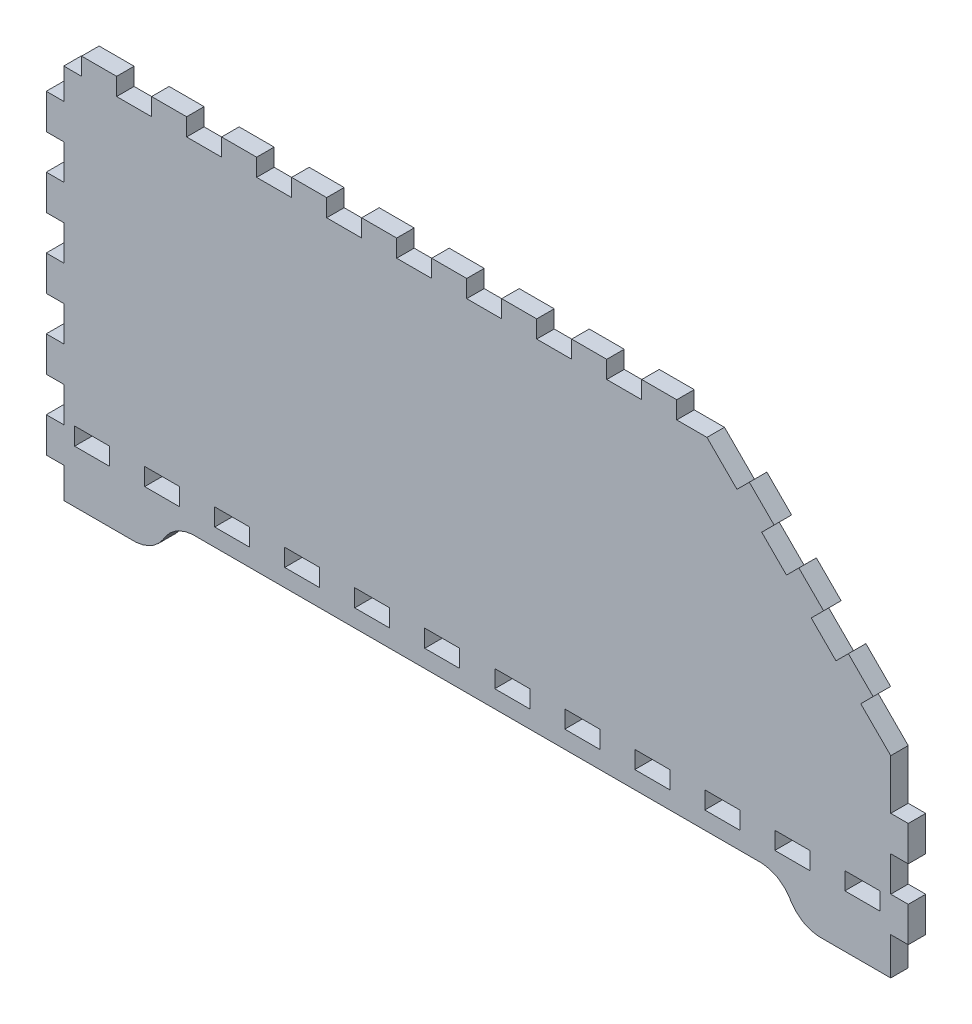
SolidWorks part; units mm, degrees
ref_plane "Front Plane" through (0, 0, 0) normal (0, 0, 1) x (1, 0, 0)
ref_plane "Top Plane" through (0, 0, 0) normal (0, 1, 0) x (1, 0, 0)
ref_plane "Right Plane" through (0, 0, 0) normal (1, 0, 0) x (0, 0, -1)
sketch "Model" plane through (0, 0, 0) normal (0, 0, 1) x (1, 0, 0)
  line L4 (25.3848, 40.3461) -> (19.6701, 40.3461)
  line L5 (19.6701, 40.3461) -> (19.6701, 46.0609)
  line L6 (19.6701, 46.0609) -> (31.0995, 46.0609)
  line L7 (31.0995, 46.0609) -> (31.0995, 40.3461)
  line L8 (31.0995, 40.3461) -> (25.3848, 40.3461)
  line L9 (48.2453, 40.3461) -> (42.5305, 40.3461)
  line L10 (42.5305, 40.3461) -> (42.5305, 46.0609)
  line L11 (42.5305, 46.0609) -> (53.9598, 46.0609)
  line L12 (53.9598, 46.0609) -> (53.9598, 40.3461)
  line L13 (53.9598, 40.3461) -> (48.2453, 40.3461)
  line L14 (71.1055, 40.3461) -> (65.3905, 40.3461)
  line L15 (65.3905, 40.3461) -> (65.3905, 46.0609)
  line L16 (65.3905, 46.0609) -> (76.8203, 46.0609)
  line L17 (76.8203, 46.0609) -> (76.8203, 40.3461)
  line L18 (76.8203, 40.3461) -> (71.1055, 40.3461)
  line L19 (93.9655, 40.3461) -> (88.2495, 40.3461)
  line L20 (88.2495, 40.3461) -> (88.2495, 46.0609)
  line L21 (88.2495, 46.0609) -> (99.6805, 46.0609)
  line L22 (99.6805, 46.0609) -> (99.6805, 40.3461)
  line L23 (99.6805, 40.3461) -> (93.9655, 40.3461)
  line L24 (116.8245, 40.3461) -> (111.1098, 40.3461)
  line L25 (111.1098, 40.3461) -> (111.1098, 46.0609)
  line L26 (111.1098, 46.0609) -> (122.5405, 46.0609)
  line L27 (122.5405, 46.0609) -> (122.5405, 40.3461)
  line L28 (122.5405, 40.3461) -> (116.8245, 40.3461)
  line L29 (139.6848, 40.3461) -> (133.9703, 40.3461)
  line L30 (133.9703, 40.3461) -> (133.9703, 46.0609)
  line L31 (133.9703, 46.0609) -> (145.3995, 46.0609)
  line L32 (145.3995, 46.0609) -> (145.3995, 40.3461)
  line L33 (145.3995, 40.3461) -> (139.6848, 40.3461)
  line L34 (162.5453, 40.3461) -> (156.8305, 40.3461)
  line L35 (156.8305, 40.3461) -> (156.8305, 46.0609)
  line L36 (156.8305, 46.0609) -> (168.2598, 46.0609)
  line L37 (168.2598, 46.0609) -> (168.2598, 40.3461)
  line L38 (168.2598, 40.3461) -> (162.5453, 40.3461)
  line L39 (185.4055, 40.3461) -> (179.6905, 40.3461)
  line L40 (179.6905, 40.3461) -> (179.6905, 46.0609)
  line L41 (179.6905, 46.0609) -> (191.1203, 46.0609)
  line L42 (191.1203, 46.0609) -> (191.1203, 40.3461)
  line L43 (191.1203, 40.3461) -> (185.4055, 40.3461)
  line L44 (208.2655, 40.3461) -> (202.5495, 40.3461)
  line L45 (202.5495, 40.3461) -> (202.5495, 46.0609)
  line L46 (202.5495, 46.0609) -> (213.9805, 46.0609)
  line L47 (213.9805, 46.0609) -> (213.9805, 40.3461)
  line L48 (213.9805, 40.3461) -> (208.2655, 40.3461)
  line L49 (231.1245, 40.3461) -> (225.4098, 40.3461)
  line L50 (225.4098, 40.3461) -> (225.4098, 46.0609)
  line L51 (225.4098, 46.0609) -> (236.8405, 46.0609)
  line L52 (236.8405, 46.0609) -> (236.8405, 40.3461)
  line L53 (236.8405, 40.3461) -> (231.1245, 40.3461)
  line L54 (253.9848, 40.3461) -> (248.2703, 40.3461)
  line L55 (248.2703, 40.3461) -> (248.2703, 46.0609)
  line L56 (248.2703, 46.0609) -> (259.6998, 46.0609)
  line L57 (259.6998, 46.0609) -> (259.6998, 40.3461)
  line L58 (259.6998, 40.3461) -> (253.9848, 40.3461)
  line L59 (276.8448, 40.3461) -> (271.1298, 40.3461)
  line L60 (271.1298, 40.3461) -> (271.1298, 46.0609)
  line L61 (271.1298, 46.0609) -> (282.5598, 46.0609)
  line L62 (282.5598, 46.0609) -> (282.5598, 40.3461)
  line L63 (282.5598, 40.3461) -> (276.8448, 40.3461)
  line L64 (16.1148, 23.2006) -> (38.9748, 23.2006)
  line L65 (38.9748, 23.2006) -> (39.7137, 23.2006)
  line L66 (39.7137, 23.2006) -> (41.9321, 23.5906)
  line L67 (41.9321, 23.5906) -> (44.2542, 24.4809)
  line L68 (44.2542, 24.4809) -> (44.6898, 24.7316)
  line L69 (44.6898, 24.7316) -> (45.1239, 24.9838)
  line L70 (45.1239, 24.9838) -> (47.056, 26.5494)
  line L71 (47.056, 26.5494) -> (48.6227, 28.4813)
  line L72 (48.6227, 28.4813) -> (48.8734, 28.9154)
  line L73 (48.8734, 28.9154) -> (49.1244, 29.3507)
  line L74 (49.1244, 29.3507) -> (50.69, 31.2829)
  line L75 (50.69, 31.2829) -> (52.6217, 32.8483)
  line L76 (52.6217, 32.8483) -> (53.057, 33.099)
  line L77 (53.057, 33.099) -> (53.4914, 33.3499)
  line L78 (53.4914, 33.3499) -> (55.8132, 34.2415)
  line L79 (55.8132, 34.2415) -> (58.0319, 34.6301)
  line L80 (58.0319, 34.6301) -> (58.772, 34.6301)
  line L81 (58.772, 34.6301) -> (243.458, 34.6301)
  line L82 (243.458, 34.6301) -> (244.1966, 34.6301)
  line L83 (244.1966, 34.6301) -> (246.4153, 34.2415)
  line L84 (246.4153, 34.2415) -> (248.7374, 33.3499)
  line L85 (248.7374, 33.3499) -> (249.1725, 33.099)
  line L86 (249.1725, 33.099) -> (249.6068, 32.8483)
  line L87 (249.6068, 32.8483) -> (251.5387, 31.2829)
  line L88 (251.5387, 31.2829) -> (253.1057, 29.3507)
  line L89 (253.1057, 29.3507) -> (253.3566, 28.9154)
  line L90 (253.3566, 28.9154) -> (253.6073, 28.4813)
  line L91 (253.6073, 28.4813) -> (255.1735, 26.5494)
  line L92 (255.1735, 26.5494) -> (257.1039, 24.9838)
  line L93 (257.1039, 24.9838) -> (257.5408, 24.7316)
  line L94 (257.5408, 24.7316) -> (257.9751, 24.4809)
  line L95 (257.9751, 24.4809) -> (260.2967, 23.5906)
  line L96 (260.2967, 23.5906) -> (262.5141, 23.2006)
  line L97 (262.5141, 23.2006) -> (263.2558, 23.2006)
  line L98 (263.2558, 23.2006) -> (286.1158, 23.2006)
  line L99 (286.1158, 23.2006) -> (286.1158, 35.465)
  line L100 (286.1158, 35.465) -> (291.8308, 35.465)
  line L101 (291.8308, 35.465) -> (291.8308, 46.8948)
  line L102 (291.8308, 46.8948) -> (286.1158, 46.8948)
  line L103 (286.1158, 46.8948) -> (286.1158, 58.324)
  line L104 (286.1158, 58.324) -> (291.8308, 58.324)
  line L105 (291.8308, 58.324) -> (291.8308, 69.7547)
  line L106 (291.8308, 69.7547) -> (286.1158, 69.7547)
  line L107 (286.1158, 69.7547) -> (286.1158, 86.0613)
  line L108 (286.1158, 86.0613) -> (276.3215, 95.855)
  line L109 (276.3215, 95.855) -> (280.3627, 99.8967)
  line L110 (280.3627, 99.8967) -> (272.2804, 107.979)
  line L111 (272.2804, 107.979) -> (268.2367, 103.9371)
  line L112 (268.2367, 103.9371) -> (260.1544, 112.0193)
  line L113 (260.1544, 112.0193) -> (264.1981, 116.061)
  line L114 (264.1981, 116.061) -> (256.1158, 124.1417)
  line L115 (256.1158, 124.1417) -> (252.0734, 120.1014)
  line L116 (252.0734, 120.1014) -> (243.9927, 128.1836)
  line L117 (243.9927, 128.1836) -> (248.033, 132.2243)
  line L118 (248.033, 132.2243) -> (239.951, 140.3078)
  line L119 (239.951, 140.3078) -> (235.9091, 136.2662)
  line L120 (235.9091, 136.2662) -> (226.1154, 146.0609)
  line L121 (226.1154, 146.0609) -> (216.2485, 146.0609)
  line L122 (216.2485, 146.0609) -> (216.2485, 151.7757)
  line L123 (216.2485, 151.7757) -> (204.8193, 151.7757)
  line L124 (204.8193, 151.7757) -> (204.8193, 146.0609)
  line L125 (204.8193, 146.0609) -> (193.3885, 146.0609)
  line L126 (193.3885, 146.0609) -> (193.3885, 151.7757)
  line L127 (193.3885, 151.7757) -> (181.959, 151.7757)
  line L128 (181.959, 151.7757) -> (181.959, 146.0609)
  line L129 (181.959, 146.0609) -> (170.5295, 146.0609)
  line L130 (170.5295, 146.0609) -> (170.5295, 151.7757)
  line L131 (170.5295, 151.7757) -> (159.0985, 151.7757)
  line L132 (159.0985, 151.7757) -> (159.0985, 146.0609)
  line L133 (159.0985, 146.0609) -> (147.6692, 146.0609)
  line L134 (147.6692, 146.0609) -> (147.6692, 151.7757)
  line L135 (147.6692, 151.7757) -> (136.2385, 151.7757)
  line L136 (136.2385, 151.7757) -> (136.2385, 146.0609)
  line L137 (136.2385, 146.0609) -> (124.809, 146.0609)
  line L138 (124.809, 146.0609) -> (124.809, 151.7757)
  line L139 (124.809, 151.7757) -> (113.3795, 151.7757)
  line L140 (113.3795, 151.7757) -> (113.3795, 146.0609)
  line L141 (113.3795, 146.0609) -> (101.9485, 146.0609)
  line L142 (101.9485, 146.0609) -> (101.9485, 151.7757)
  line L143 (101.9485, 151.7757) -> (90.5192, 151.7757)
  line L144 (90.5192, 151.7757) -> (90.5192, 146.0609)
  line L145 (90.5192, 146.0609) -> (79.0885, 146.0609)
  line L146 (79.0885, 146.0609) -> (79.0885, 151.7757)
  line L147 (79.0885, 151.7757) -> (67.659, 151.7757)
  line L148 (67.659, 151.7757) -> (67.659, 146.0609)
  line L149 (67.659, 146.0609) -> (56.2295, 146.0609)
  line L150 (56.2295, 146.0609) -> (56.2295, 151.7757)
  line L151 (56.2295, 151.7757) -> (44.7985, 151.7757)
  line L152 (44.7985, 151.7757) -> (44.7985, 146.0609)
  line L153 (44.7985, 146.0609) -> (33.3692, 146.0609)
  line L154 (33.3692, 146.0609) -> (33.3692, 151.7757)
  line L155 (33.3692, 151.7757) -> (21.9384, 151.7757)
  line L156 (21.9384, 151.7757) -> (21.9384, 146.0609)
  line L157 (21.9384, 146.0609) -> (16.1148, 146.0609)
  line L158 (16.1148, 146.0609) -> (16.1148, 136.066)
  line L159 (16.1148, 136.066) -> (10.4001, 136.066)
  line L160 (10.4001, 136.066) -> (10.4001, 124.6353)
  line L161 (10.4001, 124.6353) -> (16.1148, 124.6353)
  line L162 (16.1148, 124.6353) -> (16.1148, 113.2058)
  line L163 (16.1148, 113.2058) -> (10.4001, 113.2058)
  line L164 (10.4001, 113.2058) -> (10.4001, 101.775)
  line L165 (10.4001, 101.775) -> (16.1148, 101.775)
  line L166 (16.1148, 101.775) -> (16.1148, 90.3458)
  line L167 (16.1148, 90.3458) -> (10.4001, 90.3458)
  line L168 (10.4001, 90.3458) -> (10.4001, 78.916)
  line L169 (10.4001, 78.916) -> (16.1148, 78.916)
  line L170 (16.1148, 78.916) -> (16.1148, 67.4853)
  line L171 (16.1148, 67.4853) -> (10.4001, 67.4853)
  line L172 (10.4001, 67.4853) -> (10.4001, 56.0558)
  line L173 (10.4001, 56.0558) -> (16.1148, 56.0558)
  line L174 (16.1148, 56.0558) -> (16.1148, 44.625)
  line L175 (16.1148, 44.625) -> (10.4001, 44.625)
  line L176 (10.4001, 44.625) -> (10.4001, 33.1955)
  line L177 (10.4001, 33.1955) -> (16.1148, 33.1955)
  line L178 (16.1148, 33.1955) -> (16.1148, 23.2006)
extrude "Boss-Extrude1" add sketch "Model" along normal blind 5.715
